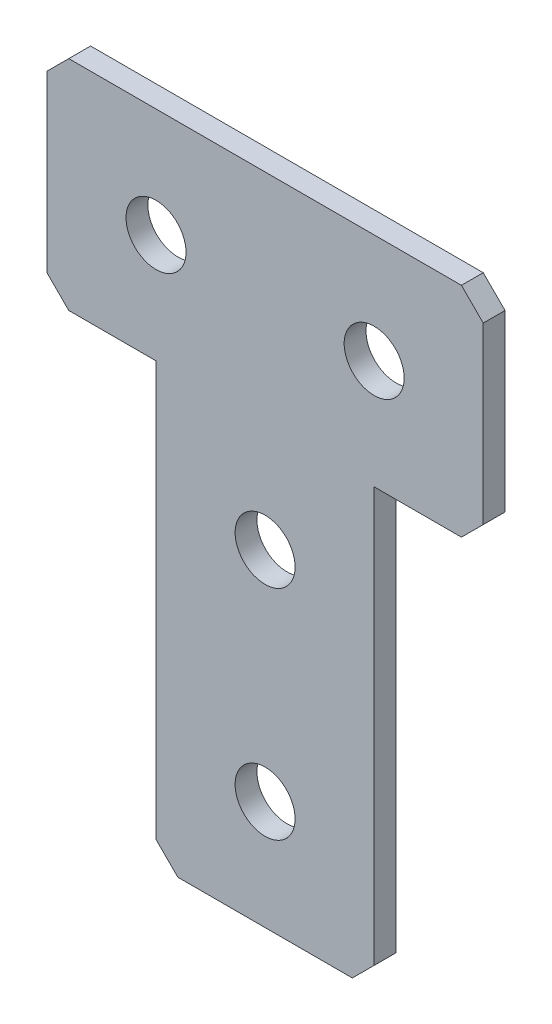
SolidWorks part; units mm, degrees
material "Простая углеродистая сталь"
ref_plane "Спереди(Плоскость XY)" through (0, 0, 0) normal (0, 0, 1) x (1, 0, 0)
ref_plane "Сверху(Плоскость XZ)" through (0, 0, 0) normal (0, 1, 0) x (1, 0, 0)
ref_plane "Справа(Плоскость ZY)" through (0, 0, 0) normal (1, 0, 0) x (0, 0, -1)
sketch "Эскиз1" plane through (0, 0, 0) normal (0, 0, -1) x (1, 0, 0)
  line L5 (10, 0) -> (-10, 0)
  line L9 (-20, -50) -> (20, -50) construction
  line L11 (0, 0) -> (0, -60) construction
  line L12 (-10, -40) -> (-10, 0)
  line L13 (-20, -40) -> (-10, -40)
  line L14 (-20, -60) -> (-20, -40)
  line L15 (10, -40) -> (10, 0)
  line L16 (20, -40) -> (10, -40)
  line L17 (20, -60) -> (20, -40)
  line L18 (-20, -60) -> (20, -60)
  dimension "D1" = 20
  dimension "D2" = 40
  dimension "D3" = 20
  dimension "D4" = 40
extrude "Бобышка-Вытянуть1" add sketch "Эскиз1" along normal blind 2
chamfer "Фаска1" distance 2 angle 45 6 edges at (10, 0, -1) (-10, 0, -1) (-20, 40, -1) (-20, 60, -1) (20, 60, -1) (20, 40, -1)
hole_wizard "Отверстие с зазором M51" positions "Эскиз2" profile "Эскиз3" hole size "M5" standard "DIN" end condition through all
sketch "Эскиз2" plane through (0, 0, 0) normal (0, 0, 1) x (1, 0, 0)
  line L0 (0, 0) -> (0, 10) construction
  line L1 (0, 10) -> (0, 30) construction
  line L2 (0, 30) -> (0, 50) construction
  line L4 (-10, 50) -> (10, 50) construction
  point P0 (-10, 50)
  point P2 (10, 50)
  point P4 (0, 30)
  point P6 (0, 10)
  dimension "D1" = 10
  dimension "D2" = 20
sketch "Эскиз3" plane through (-10, 50, 0) normal (1, 0, 0) x (0, -1, 0)
  line L0 (0, 0) -> (0, 2)
  line L1 (0, 2) -> (2.75, 2)
  line L2 (2.75, 2) -> (2.75, 0)
  line L5 (2.75, 0) -> (0, 0)
  line L11 (0, -6.35) -> (0, 107.95) construction
  dimension "Диаметр сквозного отверстия" = 5.5
  dimension "Глубина сквозного отверстия" = 2
